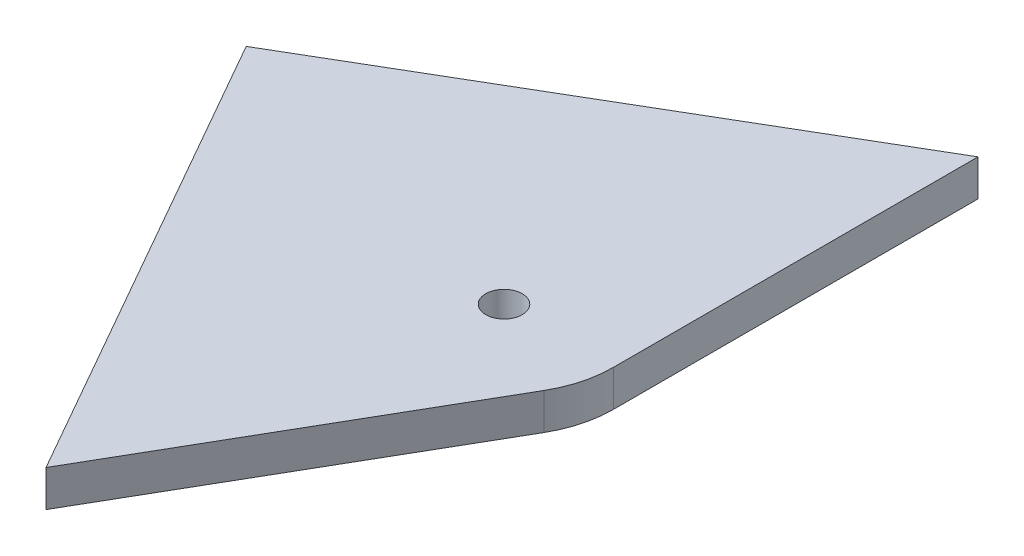
SolidWorks part; units mm, degrees
ref_plane "Plan de face" through (0, 0, 0) normal (0, 0, 1) x (1, 0, 0)
ref_plane "Plan de dessus" through (0, 0, 0) normal (0, 1, 0) x (1, 0, 0)
ref_plane "Plan de droite" through (0, 0, 0) normal (1, 0, 0) x (0, 0, -1)
sketch "Esquisse1" plane through (0, 0, 0) normal (0, 1, 0) x (1, 0, 0)
  line L0 (0, 0) -> (6, 0) construction
  line L1 (6, 0) -> (6, 20)
  line L2 (0, 0) -> (5.1962, -3) construction
  line L3 (5.1962, -3) -> (-4.8038, -20.3205)
  line L4 (5.7956, -1.5529) -> (0, 0) construction
  line L5 (0, 0) -> (-19.3185, 5.1764) construction
  line L6 (-4.8038, -20.3205) -> (-19.3185, 5.1764)
  line L7 (-19.3185, 5.1764) -> (6, 20)
  circle A0 centre (0, 0) radius 1
  arc A1 (6, 0) -> (5.1962, -3) centre (0, 0) cw
  point P6 (5.7956, -1.5529)
  point P10 (0, 0)
  dimension "D1" = 2
  dimension "D5" = 30
  dimension "D2" = 6
  dimension "D3" = 20
  dimension "D4" = 20
extrude "Boss.-Extru.1" add sketch "Esquisse1" along normal blind 2
